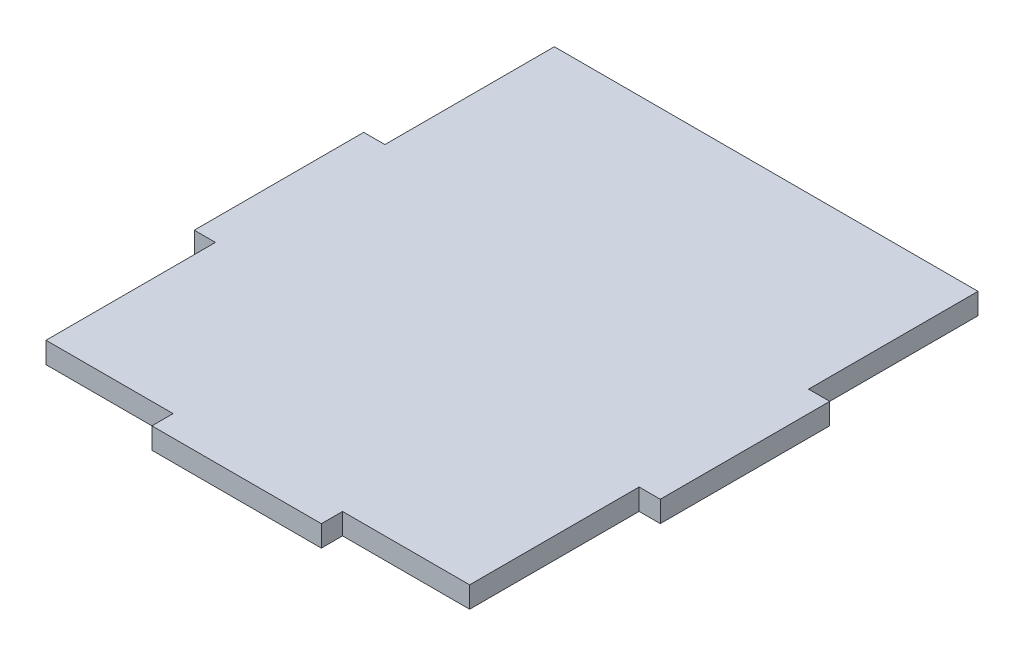
SolidWorks part; units mm, degrees
ref_plane "Front Plane" through (0, 0, 0) normal (0, 0, 1) x (1, 0, 0)
ref_plane "Top Plane" through (0, 0, 0) normal (0, 1, 0) x (1, 0, 0)
ref_plane "Right Plane" through (0, 0, 0) normal (1, 0, 0) x (0, 0, -1)
sketch "Sketch1" plane through (0, 0, 0) normal (0, 1, 0) x (1, 0, 0)
  line L0 (-69.85, 0) -> (69.85, 0) construction
  line L1 (69.85, -79.375) -> (-69.85, -79.375)
  line L2 (69.85, -79.375) -> (69.85, 79.375)
  line L3 (69.85, 79.375) -> (-69.85, 79.375)
  line L4 (-69.85, -79.375) -> (-69.85, 79.375)
  line L5 (69.85, -79.375) -> (-69.85, 79.375) construction
  line L6 (69.85, 79.375) -> (-69.85, -79.375) construction
  line L7 (-69.85, -79.375) -> (-63.5, -79.375)
  line L8 (-69.85, -79.375) -> (-69.85, -22.225)
  line L9 (-69.85, -22.225) -> (-63.5, -22.225)
  line L10 (-63.5, -79.375) -> (-63.5, -22.225)
  line L11 (0, 79.375) -> (0, -79.375) construction
  line L12 (69.85, -22.225) -> (63.5, -22.225)
  line L13 (-69.85, 28.575) -> (-63.5, 28.575)
  line L14 (-69.85, 28.575) -> (-69.85, 79.375)
  line L15 (-69.85, 79.375) -> (-63.5, 79.375)
  line L16 (-63.5, 28.575) -> (-63.5, 79.375)
  line L17 (63.5, -79.375) -> (63.5, -22.225)
  line L18 (69.85, -79.375) -> (63.5, -79.375)
  line L19 (69.85, -79.375) -> (69.85, -22.225)
  line L20 (69.85, 79.375) -> (63.5, 79.375)
  line L21 (63.5, 28.575) -> (63.5, 79.375)
  line L22 (69.85, 28.575) -> (63.5, 28.575)
  line L23 (69.85, 28.575) -> (69.85, 79.375)
  point P0 (0, 0)
  dimension "D1" = 158.75
  dimension "D2" = 139.7
  dimension "D3" = 6.35
  dimension "D4" = 57.15
  dimension "D5" = 50.8
  dimension "D6" = 6.35
extrude "Boss-Extrude1" add sketch "Sketch1" along normal blind 6.35 contours L2 L22 L21 L3 L16 L13 L4 L9 L10 L1 L17 L12
sketch "Sketch2" plane through (0, 6.35, 0) normal (0, 1, 0) x (1, 0, 0)
  line L0 (0, 79.375) -> (0, -79.375) construction
  line L1 (-63.5, -79.375) -> (-25.4, -79.375)
  line L2 (-63.5, -79.375) -> (-63.5, -73.025)
  line L3 (-63.5, -73.025) -> (-25.4, -73.025)
  line L4 (-25.4, -79.375) -> (-25.4, -73.025)
  line L5 (63.5, 79.375) -> (-63.5, 79.375) construction
  line L6 (63.5, -79.375) -> (-63.5, -79.375) construction
  line L7 (63.5, -73.025) -> (25.4, -73.025)
  line L8 (25.4, -79.375) -> (25.4, -73.025)
  line L9 (63.5, -79.375) -> (25.4, -79.375)
  line L10 (63.5, -79.375) -> (63.5, -73.025)
  dimension "D1" = 38.1
  dimension "D2" = 6.35
extrude "Cut-Extrude1" cut sketch "Sketch2" against normal blind 13.97 and the other way blind 6.35
